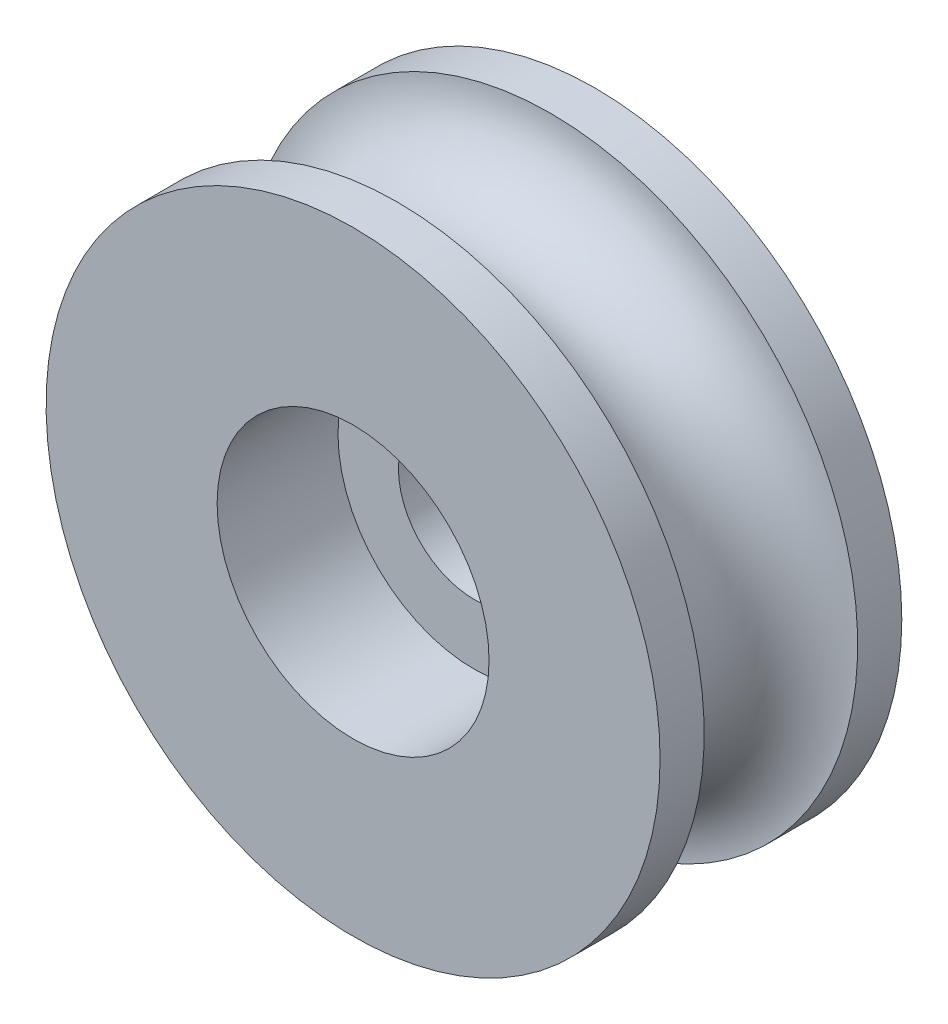
SolidWorks part; units mm, degrees
other "Markup1"
sketch "Sketch3" plane through (-10.16, 10.16, 4) normal (-0.75, 0.289, 0.595) x (0.6357, 0.0663, 0.7691)
sketch "Sketch4" plane through (-10.16, 10.16, 4) normal (-0.75, 0.289, 0.595) x (0.6357, 0.0663, 0.7691)
sketch "Sketch7" plane through (-10.16, 10.16, 8) normal (-0.75, 0.289, 0.595) x (0.6357, 0.0663, 0.7691)
ref_plane "Front Plane" through (0, 0, 0) normal (0, 0, 1) x (1, 0, 0)
ref_plane "Top Plane" through (0, 0, 0) normal (0, 1, 0) x (1, 0, 0)
ref_plane "Right Plane" through (0, 0, 0) normal (1, 0, 0) x (0, 0, -1)
sketch "Sketch1" plane through (0, 0, 0) normal (0, 0, 1) x (1, 0, 0)
  circle A0 centre (0, 0) radius 10.16
  circle A1 centre (0, 0) radius 4.5
  dimension "D1" = 20.32
  dimension "D2" = 9
extrude "Boss-Extrude1" add sketch "Sketch1" along normal blind 8
sketch "Sketch2" plane through (0, 0, 0) normal (1, 0, 0) x (0, 0, -1)
  line L0 (0, 10.16) -> (-8, 10.16) construction
  line L1 (-6.54, 10.16) -> (-1.46, 10.16)
  line L2 (0, 0) -> (-8, 0) construction
  line L3 (-8, 10.16) -> (-8, -10.16) construction
  line L4 (-4, 7.62) -> (-4, 10.16) construction
  line L5 (-4, 2.54) -> (-4, 0) construction
  line L6 (-4, -10.16) -> (-4, -7.62) construction
  line L7 (-8, -10.16) -> (0, -10.16) construction
  arc A0 (-6.54, 10.16) -> (-1.46, 10.16) centre (-4, 10.16) ccw
  point P11 (-4, 8.89)
  point P12 (-4, 2.54)
  point P15 (-4, 1.27)
  point P20 (-4, -8.89)
  dimension "D1" = 17.78
revolve "Cut-Revolve1" cut sketch "Sketch2" angle 360 about L2
sketch "Sketch5" plane through (0, 0, 0) normal (0, 0, -1) x (-1, 0, 0)
  line L0 (-10.16, 0) -> (10.16, 0) construction
  circle A0 centre (0, 0) radius 10.16 construction
sketch "Sketch6" plane through (0, 0, 0) normal (0, 0, -1) x (-1, 0, 0)
  circle A0 centre (0, 0) radius 4.5
  circle A1 centre (0, 0) radius 4.5 construction
  circle A2 centre (0, 0) radius 2.5
  dimension "D1" = 5
extrude "Boss-Extrude2" add sketch "Sketch6" against normal blind 4
